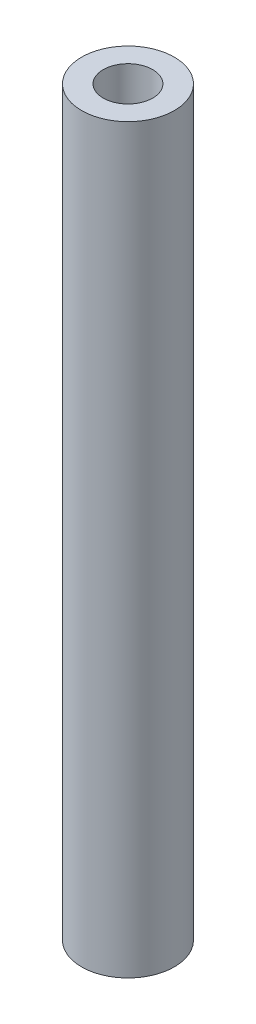
SolidWorks part; units mm, degrees
ref_plane "Front Plane" through (0, 0, 0) normal (0, 0, 1) x (1, 0, 0)
ref_plane "Top Plane" through (0, 0, 0) normal (0, 1, 0) x (1, 0, 0)
ref_plane "Right Plane" through (0, 0, 0) normal (1, 0, 0) x (0, 0, -1)
sketch "Sketch1" plane through (0, 0, 0) normal (0, 1, 0) x (1, 0, 0)
  circle A0 centre (0, 0) radius 7.5
  dimension "D1" = 15
extrude "Boss-Extrude1" add sketch "Sketch1" along normal blind 120
sketch "Sketch2" plane through (0, 0, 0) normal (0, -1, 0) x (1, 0, 0)
  circle A0 centre (0, 0) radius 5
  dimension "D1" = 10
extrude "Cut-Extrude1" cut sketch "Sketch2" against normal blind 15
sketch "Sketch3" plane through (0, 0, 0) normal (0, 0, 1) x (1, 0, 0)
  line L0 (0, 120) -> (0, -0.3161) construction
  line L1 (7.5, 120) -> (-7.5, 120) construction
  line L2 (-7.5, 0) -> (7.5, 0) construction
  circle A0 centre (0, 10) radius 3
  dimension "D1" = 10
extrude "Cut-Extrude4" cut sketch "Sketch3" against normal blind 10
sketch "Sketch4" plane through (0, 120, 0) normal (0, 1, 0) x (1, 0, 0)
  circle A0 centre (0, 0) radius 4
  dimension "D1" = 8
extrude "Cut-Extrude5" cut sketch "Sketch4" against normal blind 12
